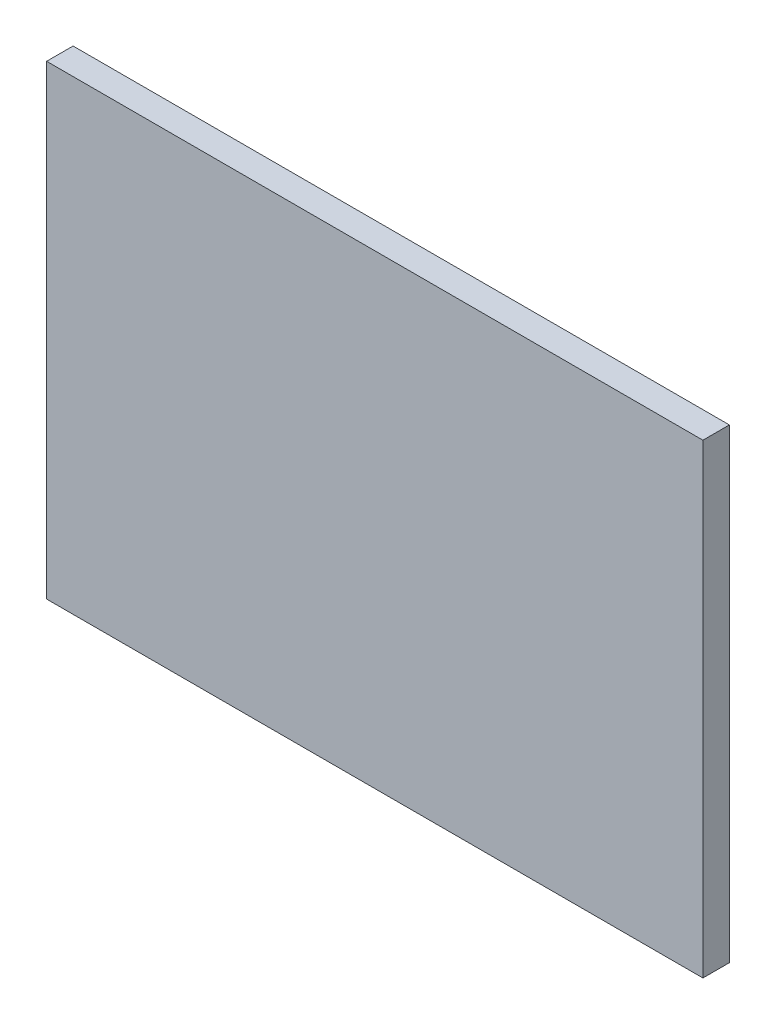
SolidWorks part; units mm, degrees
ref_plane "Front Plane" through (0, 0, 0) normal (0, 0, 1) x (1, 0, 0)
ref_plane "Top Plane" through (0, 0, 0) normal (0, 1, 0) x (1, 0, 0)
ref_plane "Right Plane" through (0, 0, 0) normal (1, 0, 0) x (0, 0, -1)
sketch "Sketch1" plane through (0, 0, 0) normal (0, 0, 1) x (1, 0, 0)
  line L1 (0, 0) -> (787.4, 0)
  line L2 (0, 0) -> (0, 558.8)
  line L3 (0, 558.8) -> (787.4, 558.8)
  line L4 (787.4, 0) -> (787.4, 558.8)
  dimension "D1" = 558.8
  dimension "D2" = 787.4
extrude "Boss-Extrude1" add sketch "Sketch1" along normal blind 31.75
